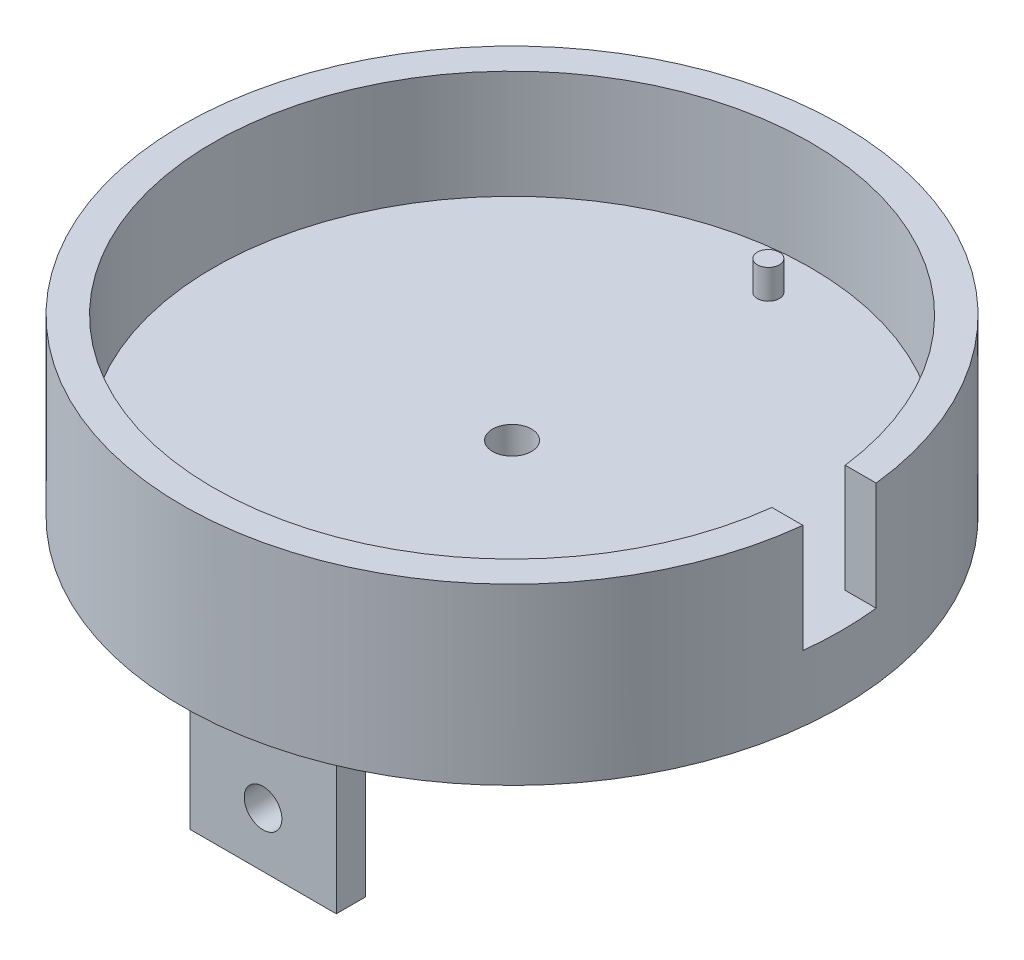
SolidWorks part; units mm, degrees
ref_plane "Front Plane" through (0, 0, 0) normal (0, 0, 1) x (1, 0, 0)
ref_plane "Top Plane" through (0, 0, 0) normal (0, 1, 0) x (1, 0, 0)
ref_plane "Right Plane" through (0, 0, 0) normal (1, 0, 0) x (0, 0, -1)
sketch "Sketch1" plane through (0, 0, 0) normal (0, 0, 1) x (1, 0, 0)
  line L0 (0, 0) -> (0, 120.0887) construction
  line L1 (0, 0) -> (57.15, 0)
  line L2 (57.15, 0) -> (57.15, 30.226)
  line L3 (57.15, 30.226) -> (51.816, 30.226)
  line L4 (51.816, 30.226) -> (51.816, 11.43)
  line L5 (51.816, 11.43) -> (0, 11.43)
  line L6 (0, 11.43) -> (0, 0)
  dimension "D1" = 51.816
  dimension "D2" = 11.43
  dimension "D3" = 5.334
  dimension "D4" = 18.796
revolve "Revolve1" add sketch "Sketch1" angle 360 mid plane about L0
ref_plane "Plane2" through (57.15, 0, 0) normal (1, 0, 0) x (0, 0, -1)
sketch "Sketch4" plane through (57.15, 0, 0) normal (1, 0, 0) x (0, 0, -1)
  line L0 (0, 0) -> (0, 30.226) construction
  line L1 (51.816, 30.226) -> (-51.816, 30.226) construction
  line L3 (51.816, 11.43) -> (-51.816, 11.43) construction
  line L4 (-6.35, 11.43) -> (6.35, 11.43)
  line L5 (-6.35, 11.43) -> (-6.35, 30.226)
  line L6 (-6.35, 30.226) -> (6.35, 30.226)
  line L7 (6.35, 11.43) -> (6.35, 30.226)
  line L8 (57.15, 30.226) -> (-57.15, 30.226) construction
  point P5 (0, 15.113)
  point P14 (0, 11.43)
  dimension "D1" = 12.7
extrude "Cut-Extrude2" cut sketch "Sketch4" against normal up to surface (5.7246 mm away)
sketch "Sketch5" plane through (0, 0, 0) normal (0, -1, 0) x (1, 0, 0)
  circle A0 centre (0, 0) radius 3.3782
  dimension "D1" = 6.7564
extrude "Cut-Extrude3" cut sketch "Sketch5" against normal through all
sketch "Sketch6" plane through (0, 11.43, 0) normal (0, 1, 0) x (1, 0, 0)
  line L0 (51.816, 0) -> (57.15, 0) construction
  line L1 (57.15, -15.5765) -> (57.15, 15.5765) construction
  circle A0 centre (0, 44.45) radius 1.905
  arc A1 (51.4254, 6.35) -> (51.4254, -6.35) centre (0, 0) ccw construction
  circle A2 centre (0, -44.45) radius 1.905
  dimension "D2" = 3.81
  dimension "D1" = 44.45
extrude "Boss-Extrude1" add sketch "Sketch6" along normal blind 5.08
sketch "Sketch7" plane through (0, 0, 0) normal (0, 1, 0) x (1, 0, 0)
  line L0 (-12.7, -38.1) -> (12.7, -43.18) construction
  line L1 (57.15, 0) -> (-57.15, 0) construction
  line L2 (-12.7, -38.1) -> (12.7, -38.1)
  line L3 (-12.7, -38.1) -> (-12.7, -43.18)
  line L4 (-12.7, -43.18) -> (12.7, -43.18)
  line L5 (12.7, -38.1) -> (12.7, -43.18)
  line L6 (-12.7, -43.18) -> (12.7, -38.1) construction
  line L7 (0, -57.15) -> (0, 57.15) construction
  line L8 (-12.7, 38.1) -> (12.7, 38.1)
  line L9 (-12.7, 38.1) -> (-12.7, 43.18)
  line L10 (-12.7, 43.18) -> (12.7, 38.1) construction
  line L11 (-12.7, 38.1) -> (12.7, 43.18) construction
  line L12 (-12.7, 43.18) -> (12.7, 43.18)
  line L14 (12.7, 38.1) -> (12.7, 43.18)
  line L15 (-57.15, 0) -> (-57.15, 34.3333) construction
  circle A0 centre (0, 0) radius 57.15 construction
  point P1 (0, -40.64)
  point P5 (-57.15, 34.3333)
  point P6 (0, -40.64)
  point P16 (0, 40.64)
  dimension "D1" = 25.4
  dimension "D2" = 5.08
  dimension "D3" = 40.64
extrude "Boss-Extrude4" add sketch "Sketch7" against normal blind 31.75
fillet "Fillet1" radius 6.35 6 edges at (12.7, 0, -40.64) (0, 0, -43.18) (-12.7, 0, -40.64) (-12.7, 0, 40.64) (12.7, 0, 40.64) (0, 0, 43.18)
sketch "Sketch8" plane through (0, 0, 43.18) normal (0, 0, 1) x (1, 0, 0)
  line L0 (-12.7, -31.75) -> (12.7, -31.75) construction
  line L1 (-12.7, -31.75) -> (-12.7, -6.35) construction
  circle A0 centre (0, -22.225) radius 3.2639
  dimension "D1" = 6.5278
  dimension "D2" = 9.525
  dimension "D3" = 12.7
extrude "Cut-Extrude4" cut sketch "Sketch8" against normal through all both and the other way through all
ref_plane "Plane3" through (-3.8283, -14.2875, 0) normal (-0.2588, -0.9659, 0) x (0, 0, -1)
